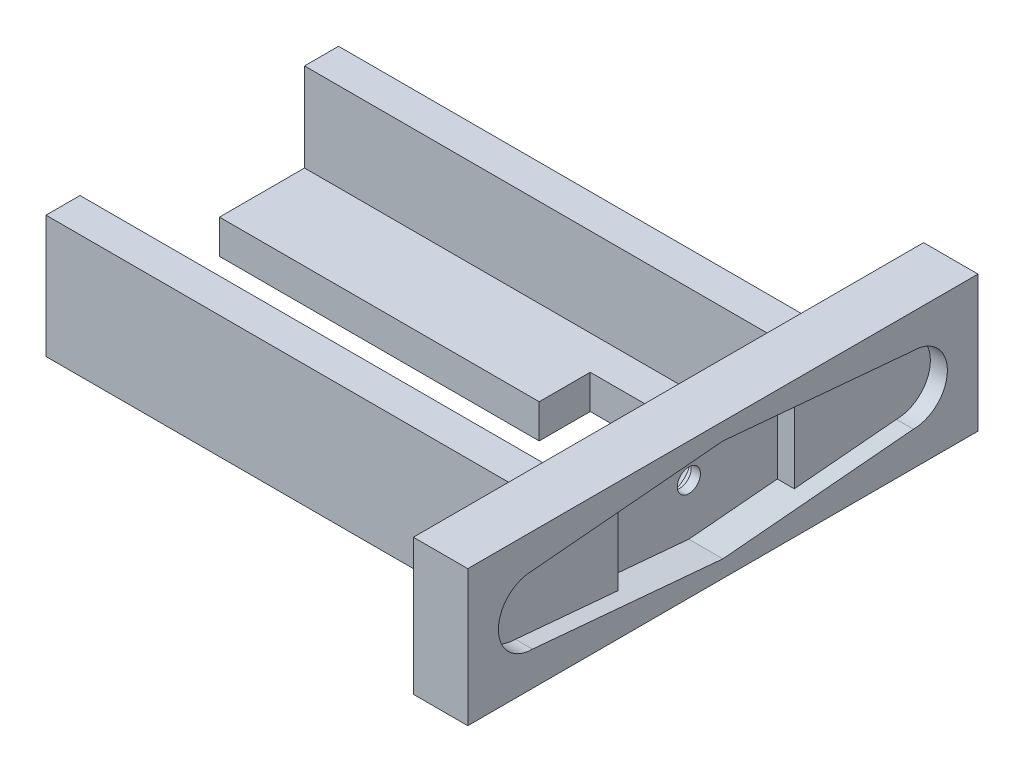
SolidWorks part; units mm, degrees
ref_plane "Front" through (0, 0, 0) normal (0, 0, 1) x (1, 0, 0)
ref_plane "Top" through (0, 0, 0) normal (0, 1, 0) x (1, 0, 0)
ref_plane "Right" through (0, 0, 0) normal (1, 0, 0) x (0, 0, -1)
sketch "草图1" plane through (0, 0, 0) normal (0, 1, 0) x (1, 0, 0)
  line L1 (0, 0) -> (10, 0)
  line L2 (0, 0) -> (0, 75)
  line L3 (0, 75) -> (10, 75)
  line L4 (10, 0) -> (10, 75)
  dimension "D1" = 75
  dimension "D2" = 10
extrude "凸台-拉伸2" add sketch "草图1" along normal blind 20 contours L3 L4 L1 L2
sketch "草图4" plane through (10, 0, 0) normal (1, 0, 0) x (0, 0, -1)
  line L0 (0, 20) -> (75, 20) construction
  line L3 (0, 20) -> (0, 0) construction
  arc A0 (20, 6.2) -> (20, 13.8) centre (20, 10) cw
  arc A1 (78, 6.2) -> (78, 13.8) centre (78, 10) ccw
  circle A2 centre (50, 10) radius 6
  dimension "D1" = 10
  dimension "D2" = 50
  dimension "D4" = 28
extrude "切除-拉伸3" cut sketch "草图4" against normal blind 2
sketch "草图5" plane through (8, 0, 0) normal (1, 0, 0) x (0, 0, -1)
  line L1 (75, 0) -> (75, 20)
  line L6 (0, 20) -> (0, 0) construction
  line L7 (9.5, 15) -> (37.5, 17.5)
  line L8 (37.5, 17.5) -> (65.5, 15)
  line L9 (65.5, 5) -> (37.5, 2.5)
  line L10 (37.5, 2.5) -> (9.5, 5)
  circle A0 centre (37.5, 10) radius 7.5
  arc A1 (9.5, 5) -> (9.5, 15) centre (9.5, 10) cw
  arc A2 (65.5, 5) -> (65.5, 15) centre (65.5, 10) ccw
  point P23 (0, 10)
  dimension "D1" = 28
  dimension "D2" = 28
  dimension "D3" = 37.5
extrude "切除-拉伸4" cut sketch "草图5" against normal blind 2.5 contours L9 A2 L8 A0 | L7 A0 L10 L9 L8 | A1 L10 A0 L7
sketch "草图6" plane through (8, 0, 0) normal (1, 0, 0) x (0, 0, -1)
  line L1 (37.5, 17.5) -> (24.5515, 16.3439)
  line L2 (9.5, 15) -> (37.5, 17.5) construction
  line L3 (24.5515, 16.3439) -> (24.5515, 3.6561)
  line L4 (37.5, 2.5) -> (9.5, 5) construction
  line L5 (24.5515, 3.6561) -> (37.5, 2.5)
  line L6 (37.5, 2.5) -> (50.5, 3.6607)
  line L7 (65.5, 5) -> (37.5, 2.5) construction
  line L8 (50.5, 3.6607) -> (50.5, 16.3393)
  line L9 (37.5, 17.5) -> (65.5, 15) construction
  line L10 (50.5, 16.3393) -> (37.5, 17.5)
  dimension "D1" = 13
  dimension "D2" = 13
extrude "切除-拉伸5" cut sketch "草图6" against normal blind 5
sketch "草图10" plane through (0, 0, 0) normal (-1, 0, 0) x (0, 0, 1)
  line L0 (-75, 20) -> (-75, 0) construction
  line L1 (-54, 5) -> (-21, 5)
  line L2 (-54, 5) -> (-54, 0)
  line L3 (-54, 0) -> (-21, 0)
  line L4 (-21, 5) -> (-21, 0)
  line L5 (0, 0) -> (-75, 0) construction
  dimension "D1" = 33
  dimension "D2" = 5
  dimension "D3" = 21
  dimension "D4" = 0
extrude "凸台-拉伸3" add sketch "草图10" along normal blind 70
sketch "草图11" plane through (0, 0, 0) normal (-1, 0, 0) x (0, 0, 1)
  line L1 (-21, 0) -> (-16, 0)
  line L2 (-21, 0) -> (-21, 18)
  line L3 (-21, 18) -> (-16, 18)
  line L4 (-16, 0) -> (-16, 18)
  dimension "D1" = 5
  dimension "D2" = 18
extrude "凸台-拉伸4" add sketch "草图11" along normal blind 70
sketch "草图12" plane through (0, 0, 0) normal (-1, 0, 0) x (0, 0, 1)
  line L1 (-54, 0) -> (-59, 0)
  line L2 (-54, 0) -> (-54, 18)
  line L3 (-54, 18) -> (-59, 18)
  line L4 (-59, 0) -> (-59, 18)
  dimension "D1" = 18
  dimension "D2" = 5
extrude "凸台-拉伸5" add sketch "草图12" along normal blind 70
sketch "草图13" plane through (0, 5, 0) normal (0, 1, 0) x (1, 0, 0)
  line L0 (-70, 21) -> (-70, 54) construction
  line L5 (-70, 41.5) -> (-10, 41.5)
  line L6 (-70, 41.5) -> (-70, 33.5)
  line L7 (-70, 33.5) -> (-10, 33.5)
  line L8 (-10, 41.5) -> (-10, 33.5)
  line L9 (-70, 54) -> (0, 54) construction
  dimension "D1" = 60
  dimension "D2" = 8
  dimension "D3" = 12.5
extrude "切除-拉伸6" cut sketch "草图13" against normal blind 20
sketch "草图14" plane through (0, 5, 0) normal (0, 1, 0) x (1, 0, 0)
  line L0 (-70, 54) -> (0, 54) construction
  line L1 (-23, 49) -> (-13, 49)
  line L2 (-23, 49) -> (-23, 27.2393)
  line L3 (-23, 27.2393) -> (-13, 27.2393)
  line L4 (-13, 49) -> (-13, 27.2393)
  line L5 (0, 21) -> (0, 54) construction
  dimension "D1" = 10
  dimension "D2" = 5
  dimension "D3" = 13
extrude "切除-拉伸7" cut sketch "草图14" against normal blind 20
hole_wizard "M3 凹圆头螺钉的柱形沉头孔1" positions "3D草图1" profile "草图15" counterbore size "M3" standard "ANSI Metric"
sketch3d "3D草图1"
  line L1 (0, 20, 0) -> (0, 20, -75) construction
  line L2 (0, 20, -75) -> (0, 0, -75) construction
  point P0 (0, 10, -37.5)
  dimension "D1" = 10
  dimension "D2" = 37.5
sketch "草图15" plane through (0, 10, -37.5) normal (0, 1, 0) x (0, 0, 1)
  line L0 (0, 0) -> (0, 21.0215)
  line L1 (0, 21.0215) -> (1.7, 20)
  line L2 (1.7, 20) -> (1.7, 1.65)
  line L3 (1.7, 1.65) -> (3.35, 1.65)
  line L4 (3.35, 1.65) -> (3.35, 0)
  line L5 (3.35, 0) -> (0, 0)
  line L10 (0, 21.0215) -> (-1.7, 20) construction
  line L11 (0, -6.35) -> (0, 107.95) construction
  dimension "孔直径" = 3.4
  dimension "孔深度" = 20
  dimension "柱形沉头孔直径" = 6.7
  dimension "柱形沉头孔深度" = 1.65
  dimension "导头角度" = 118
